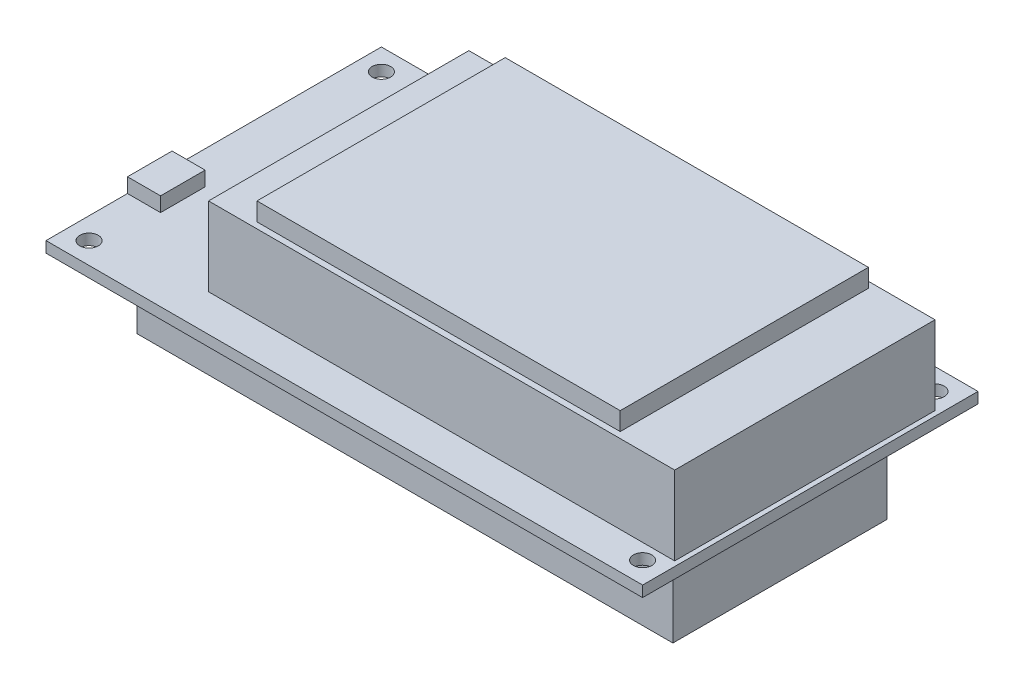
SolidWorks part; units mm, degrees
ref_plane "前视基准面" through (0, 0, 0) normal (0, 0, 1) x (1, 0, 0)
ref_plane "上视基准面" through (0, 0, 0) normal (0, 1, 0) x (1, 0, 0)
ref_plane "右视基准面" through (0, 0, 0) normal (1, 0, 0) x (0, 0, -1)
sketch "草图1" plane through (0, 0, 0) normal (0, 1, 0) x (1, 0, 0)
  line L1 (0, 0) -> (98.55, 0)
  line L2 (0, 0) -> (0, 55.4)
  line L3 (0, 55.4) -> (98.55, 55.4)
  line L4 (98.55, 0) -> (98.55, 55.4)
  circle A0 centre (3.556, 3.556) radius 1.524
  circle A1 centre (94.996, 3.556) radius 1.524
  circle A2 centre (94.996, 51.846) radius 1.524
  circle A3 centre (3.556, 51.846) radius 1.524
  point P7 (0, 0)
  point P8 (0, 0)
  point P9 (0, 0)
  point P16 (0, 0)
  dimension "D3" = 2
  dimension "D1" = 98.55
  dimension "D2" = 55.4
  dimension "D4" = 2
extrude "凸台-拉伸1" add sketch "草图1" along normal blind 1.8
sketch "草图2" plane through (0, 1.8, 0) normal (0, 1, 0) x (1, 0, 0)
  line L0 (98.55, 0) -> (98.55, 55.4) construction
  line L1 (97.75, 49.1) -> (20.75, 49.1)
  line L2 (97.75, 49.1) -> (97.75, 6.1)
  line L3 (97.75, 6.1) -> (20.75, 6.1)
  line L4 (20.75, 49.1) -> (20.75, 6.1)
  line L5 (98.55, 55.4) -> (0, 55.4) construction
  point P4 (0, 0)
  point P9 (0, 0)
  dimension "D1" = 0.8
  dimension "D2" = 6.3
  dimension "D3" = 43
extrude "凸台-拉伸2" add sketch "草图2" along normal blind 13
sketch "草图3" plane through (0, 14.8, 0) normal (0, 1, 0) x (1, 0, 0)
  line L0 (20.75, 6.1) -> (97.75, 6.1) construction
  line L1 (27.75, 48.1) -> (87.75, 48.1)
  line L2 (27.75, 48.1) -> (27.75, 7.1)
  line L3 (27.75, 7.1) -> (87.75, 7.1)
  line L4 (87.75, 48.1) -> (87.75, 7.1)
  line L5 (97.75, 49.1) -> (20.75, 49.1) construction
  line L6 (20.75, 49.1) -> (20.75, 6.1) construction
  line L7 (97.75, 6.1) -> (97.75, 49.1) construction
  dimension "D1" = 1
  dimension "D2" = 1
  dimension "D3" = 7
  dimension "D4" = 10
extrude "凸台-拉伸3" add sketch "草图3" along normal blind 3
sketch "草图4" plane through (0, 1.8, 0) normal (0, 1, 0) x (1, 0, 0)
  line L1 (0, 13.46) -> (5.46, 13.46)
  line L2 (0, 13.46) -> (0, 20.826)
  line L3 (0, 20.826) -> (5.46, 20.826)
  line L4 (5.46, 13.46) -> (5.46, 20.826)
  point P4 (0, 0)
extrude "凸台-拉伸4" add sketch "草图4" along normal blind 2.4 separate body
sketch "草图5" plane through (0, 0, 0) normal (0, -1, 0) x (1, 0, 0)
  line L0 (0, -55.4) -> (0, 0) construction
  line L1 (5, -10) -> (93.55, -10)
  line L2 (5, -10) -> (5, -45.4)
  line L3 (5, -45.4) -> (93.55, -45.4)
  line L4 (93.55, -10) -> (93.55, -45.4)
  line L5 (0, 0) -> (98.55, 0) construction
  line L6 (98.55, -55.4) -> (0, -55.4) construction
  line L7 (98.55, 0) -> (98.55, -55.4) construction
  dimension "D1" = 5
  dimension "D2" = 10
  dimension "D3" = 10
  dimension "D4" = 5
extrude "凸台-拉伸5" add sketch "草图5" along normal blind 14
